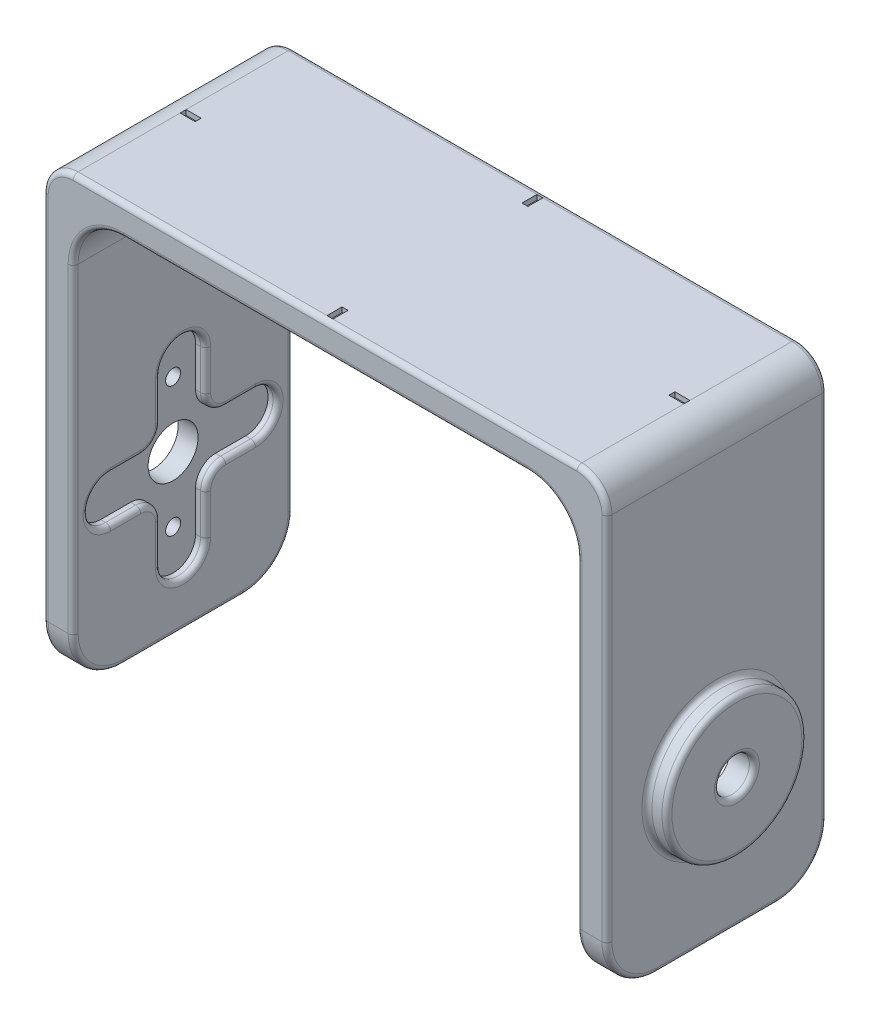
SolidWorks part; units mm, degrees
ref_plane "Front Plane" through (0, 0, 0) normal (0, 0, 1) x (1, 0, 0)
ref_plane "Top Plane" through (0, 0, 0) normal (0, 1, 0) x (1, 0, 0)
ref_plane "Right Plane" through (0, 0, 0) normal (1, 0, 0) x (0, 0, -1)
sketch "Sketch1" plane through (0, 0, 0) normal (1, 0, 0) x (0, 0, -1)
  line L1 (0, 0) -> (22, 0)
  line L2 (0, 0) -> (0, 45)
  line L3 (0, 45) -> (22, 45)
  line L4 (22, 0) -> (22, 45)
  dimension "D1" = 45
  dimension "D2" = 22
extrude "Boss-Extrude1" add sketch "Sketch1" along normal blind 3 contours L3 L4 L1 L2
sketch "Sketch2" plane through (3, 0, 0) normal (1, 0, 0) x (0, 0, -1)
  line L0 (22, 0) -> (22, 45) construction
  line L1 (0, 45) -> (22, 45)
  line L2 (0, 45) -> (0, 42)
  line L3 (0, 42) -> (22, 42)
  line L4 (22, 45) -> (22, 42)
  dimension "D1" = 3
extrude "Boss-Extrude2" add sketch "Sketch2" along normal blind 50.4
sketch "Sketch3" plane through (53.4, 0, 0) normal (1, 0, 0) x (0, 0, -1)
  line L1 (0, 45) -> (22, 45)
  line L2 (0, 45) -> (0, 0)
  line L3 (0, 0) -> (22, 0)
  line L4 (22, 45) -> (22, 0)
extrude "Boss-Extrude3" add sketch "Sketch3" along normal blind 3
sketch "Sketch4" plane through (3, 0, 0) normal (1, 0, 0) x (0, 0, -1)
  line L0 (11, 45) -> (11, 0) construction
  line L1 (22, 45) -> (0, 45) construction
  line L2 (8.75, 19.25) -> (8.75, 23.25)
  line L3 (13.25, 19.25) -> (13.25, 23.25)
  line L4 (13.25, 10.75) -> (13.25, 6.75)
  line L5 (8.75, 10.75) -> (8.75, 6.75)
  line L6 (6.75, 17.25) -> (3.75, 17.25)
  line L7 (6.75, 12.75) -> (3.75, 12.75)
  line L8 (15.25, 17.25) -> (18.25, 17.25)
  line L9 (15.25, 12.75) -> (18.25, 12.75)
  line L10 (0, 15) -> (22, 15) construction
  line L11 (0, 0) -> (22, 0) construction
  line L12 (0, 45) -> (0, 0) construction
  line L13 (22, 0) -> (22, 45) construction
  arc A0 (13.25, 23.25) -> (8.75, 23.25) centre (11, 23.25) ccw
  arc A1 (13.25, 6.75) -> (8.75, 6.75) centre (11, 6.75) cw
  arc A2 (3.75, 12.75) -> (3.75, 17.25) centre (3.75, 15) cw
  arc A3 (18.25, 12.75) -> (18.25, 17.25) centre (18.25, 15) ccw
  arc A4 (8.75, 10.75) -> (6.75, 12.75) centre (6.75, 10.75) ccw
  arc A5 (8.75, 19.25) -> (6.75, 17.25) centre (6.75, 19.25) cw
  arc A6 (13.25, 19.25) -> (15.25, 17.25) centre (15.25, 19.25) ccw
  arc A7 (13.25, 10.75) -> (15.25, 12.75) centre (15.25, 10.75) cw
  point P0 (11, 4.5)
  point P1 (20.5, 15)
  point P9 (11, 25.5)
  point P18 (1.5, 15)
  dimension "D4" = 2
  dimension "D8" = 3
  dimension "D1" = 4.5
  dimension "D2" = 4.5
  dimension "D3" = 21
  dimension "D5" = 19
  dimension "D6" = 4.5
  dimension "D7" = 4.5
  dimension "D9" = 3
  dimension "D10" = 4
  dimension "D11" = 4
  dimension "D12" = 3
  dimension "D13" = 3
  dimension "D14" = 4
  dimension "D15" = 4
  dimension "D16" = 15
extrude "Cut-Extrude1" cut sketch "Sketch4" against normal blind 1
sketch "Sketch5" plane through (2, 0, 0) normal (1, 0, 0) x (0, 0, -1)
  line L0 (11, 25.5) -> (11, 4.5) construction
  line L1 (1.5, 15) -> (20.5, 15) construction
  arc A0 (13.25, 23.25) -> (8.75, 23.25) centre (11, 23.25) ccw construction
  arc A1 (8.75, 6.75) -> (13.25, 6.75) centre (11, 6.75) ccw construction
  arc A2 (3.75, 17.25) -> (3.75, 12.75) centre (3.75, 15) ccw construction
  arc A3 (18.25, 12.75) -> (18.25, 17.25) centre (18.25, 15) ccw construction
  circle A4 centre (11, 15) radius 2.5
  circle A5 centre (11, 21.5) radius 0.75
  circle A6 centre (11, 8.5) radius 0.75
  dimension "D1" = 5
  dimension "D2" = 1.5
  dimension "D3" = 6.5
extrude "Cut-Extrude2" cut sketch "Sketch5" against normal blind 2
sketch "Sketch7" plane through (53.4, 0, 0) normal (-1, 0, 0) x (0, 0, 1)
  circle A0 centre (-11, 15) radius 5.25
  dimension "D1" = 10.5
extrude "Cut-Extrude3" cut sketch "Sketch7" against normal blind 2.5
sketch "Sketch8" plane through (56.4, 0, 0) normal (1, 0, 0) x (0, 0, -1)
  circle A0 centre (11, 15) radius 7
  dimension "D1" = 14
extrude "Boss-Extrude4" add sketch "Sketch8" along normal blind 2
sketch "Sketch9" plane through (58.4, 0, 0) normal (1, 0, 0) x (0, 0, -1)
  circle A0 centre (11, 15) radius 1.75
  dimension "D1" = 3.5
extrude "Cut-Extrude4" cut sketch "Sketch9" against normal up to next
fillet "Fillet1" radius 5 4 edges at (1.5, 0, -22) (1.5, 0, 0) (54.9, 0, 0) (54.9, 0, -22)
fillet "Fillet2" radius 5 2 edges at (3, 42, -11) (53.4, 42, -11)
fillet "Fillet3" radius 3 2 edges at (0, 45, -11) (56.4, 45, -11)
fillet "Fillet4" radius 0.5 36 edges at (56.4, 15, -18) (58.4, 15, -12.75) (58.4, 15, -18) (3, 1.4645, -1.4645) (3, 0, -11) (3, 1.4645, -20.5355) (3, 21, -22) (4.4645, 40.5355, -22) (28.2, 42, -22) (51.9355, 40.5355, -22) (53.4, 21, -22) (53.4, 1.4645, -20.5355) (53.4, 0, -11) (53.4, 1.4645, -1.4645) (56.4, 1.4645, -1.4645) (56.4, 0, -11) (56.4, 1.4645, -20.5355) (56.4, 23.5, -22) (55.5213, 44.1213, -22) (28.2, 45, -22) (0.8787, 44.1213, -22) (0, 23.5, -22) (0, 1.4645, -20.5355) (0, 0, -11) (0, 1.4645, -1.4645) (55.5213, 44.1213, 0) (56.4, 23.5, 0) (53.4, 21, 0) (51.9355, 40.5355, 0) (28.2, 42, 0) (4.4645, 40.5355, 0) (3, 21, 0) (0, 23.5, 0) (0.8787, 44.1213, 0) (28.2, 45, 0) (53.4, 15, -5.75)
fillet "Fillet5" radius 0.5 16 edges at (3, 12.1642, -13.8358) (3, 8.75, -13.25) (3, 4.5, -11) (3, 8.75, -8.75) (3, 12.1642, -8.1642) (3, 12.75, -5.25) (3, 15, -1.5) (3, 17.25, -5.25) (3, 17.8358, -8.1642) (3, 21.25, -8.75) (3, 25.5, -11) (3, 21.25, -13.25) (3, 17.8358, -13.8358) (3, 17.25, -16.75) (3, 15, -20.5) (3, 12.75, -16.75)
sketch "Sketch10" plane through (0, 45, 0) normal (0, 1, 0) x (1, 0, 0)
  line L0 (53.4, 21.5) -> (3, 21.5) construction
  line L1 (27.9, 21.5) -> (28.5, 21.5)
  line L2 (27.9, 21.5) -> (27.9, 20)
  line L3 (27.9, 20) -> (28.5, 20)
  line L4 (28.5, 21.5) -> (28.5, 20)
  line L5 (3, 11) -> (53.4, 11) construction
  line L6 (3, 21.5) -> (3, 0.5) construction
  line L7 (53.4, 0.5) -> (53.4, 21.5) construction
  line L8 (28.5, 0.5) -> (28.5, 2)
  line L9 (27.9, 2) -> (28.5, 2)
  line L10 (27.9, 0.5) -> (27.9, 2)
  line L11 (27.9, 0.5) -> (28.5, 0.5)
  line L12 (28.2, 21.5) -> (28.2, 0.5) construction
  line L13 (3, 11.3) -> (4.5, 11.3)
  line L14 (3, 11.3) -> (3, 10.7)
  line L15 (3, 10.7) -> (4.5, 10.7)
  line L16 (4.5, 11.3) -> (4.5, 10.7)
  line L17 (51.9, 11.3) -> (51.9, 10.7)
  line L18 (53.4, 10.7) -> (51.9, 10.7)
  line L19 (53.4, 11.3) -> (53.4, 10.7)
  line L20 (53.4, 11.3) -> (51.9, 11.3)
  point P6 (27.9, 20.75)
  point P7 (28.2, 21.5)
  dimension "D1" = 0.6
  dimension "D2" = 1.5
  dimension "D3" = 1.5
  dimension "D4" = 0.6
extrude "Cut-Extrude5" cut sketch "Sketch10" against normal blind 0.5
